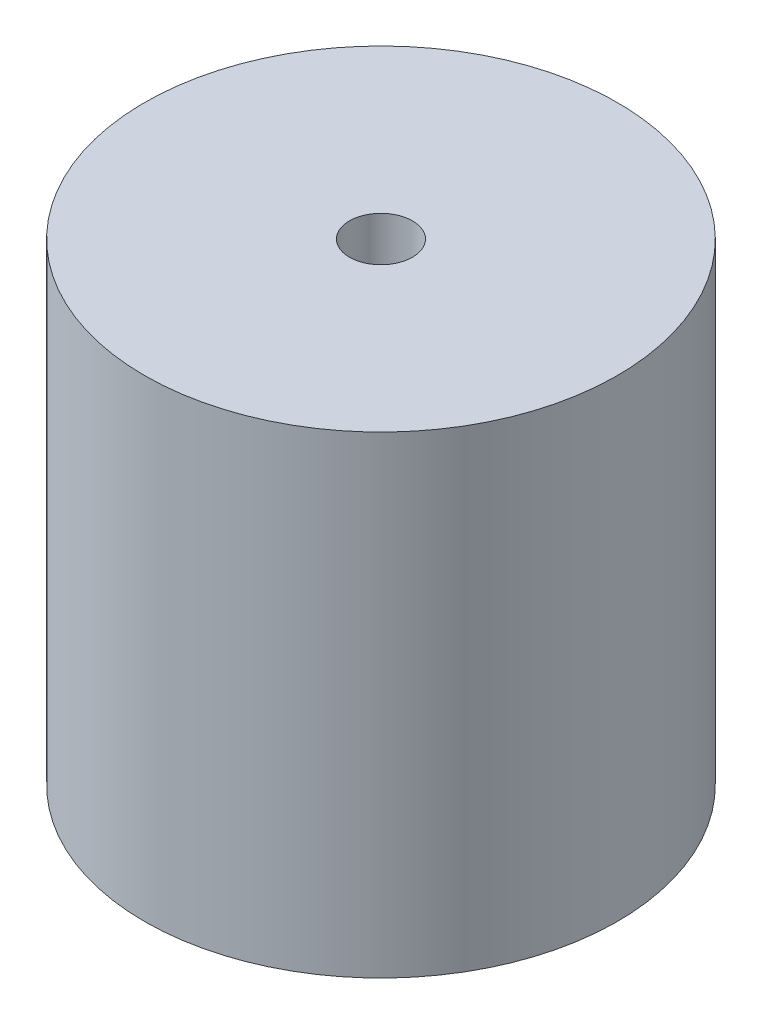
SolidWorks part; units mm, degrees
ref_plane "Front Plane" through (0, 0, 0) normal (0, 0, 1) x (1, 0, 0)
ref_plane "Top Plane" through (0, 0, 0) normal (0, 1, 0) x (1, 0, 0)
ref_plane "Right Plane" through (0, 0, 0) normal (1, 0, 0) x (0, 0, -1)
sketch "Sketch1" plane through (0, 0, 0) normal (0, 1, 0) x (1, 0, 0)
  circle A0 centre (0, 0) radius 15
extrude "Boss-Extrude1" add sketch "Sketch1" along normal blind 30
sketch "Sketch2" plane through (0, 0, 0) normal (0, 1, 0) x (1, 0, 0)
  circle A0 centre (0, 0) radius 2
extrude "Cut-Extrude1" cut sketch "Sketch2" along normal blind 30
